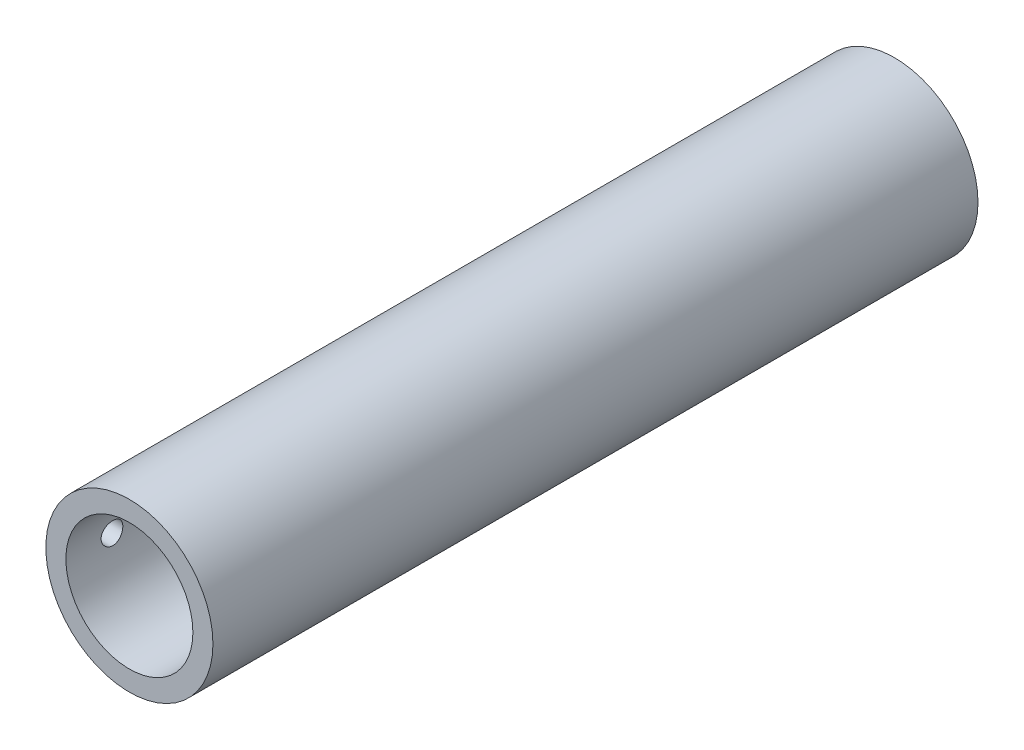
SolidWorks part; units mm, degrees
ref_plane "Front Plane" through (0, 0, 0) normal (0, 0, 1) x (1, 0, 0)
ref_plane "Top Plane" through (0, 0, 0) normal (0, 1, 0) x (1, 0, 0)
ref_plane "Right Plane" through (0, 0, 0) normal (1, 0, 0) x (0, 0, -1)
sketch "Sketch1" plane through (0, 0, 0) normal (0, 0, 1) x (1, 0, 0)
  circle A0 centre (0, 0) radius 12.7
  circle A1 centre (0, 0) radius 9.652
  dimension "D1" = 25.4
  dimension "D2" = 3.048
extrude "Boss-Extrude1" add sketch "Sketch1" along normal blind 116.3
sketch "Sketch2" plane through (0, 0, 0) normal (1, 0, 0) x (0, 0, -1)
  line L0 (-116.3, 12.7) -> (-116.3, -12.7) construction
  line L1 (-116.3, 0) -> (0, 0) construction
  line L2 (0, -12.7) -> (0, 12.7) construction
  circle A0 centre (-109.3, 0) radius 1.65
  circle A1 centre (-29.8, 0) radius 1.65
  circle A2 centre (-18, 0) radius 1.65
  dimension "D1" = 3.3
  dimension "D2" = 7
  dimension "D3" = 3.3
  dimension "D4" = 79.5
  dimension "D5" = 3.3
  dimension "D6" = 18
extrude "Cut-Extrude1" cut sketch "Sketch2" against normal blind 30
